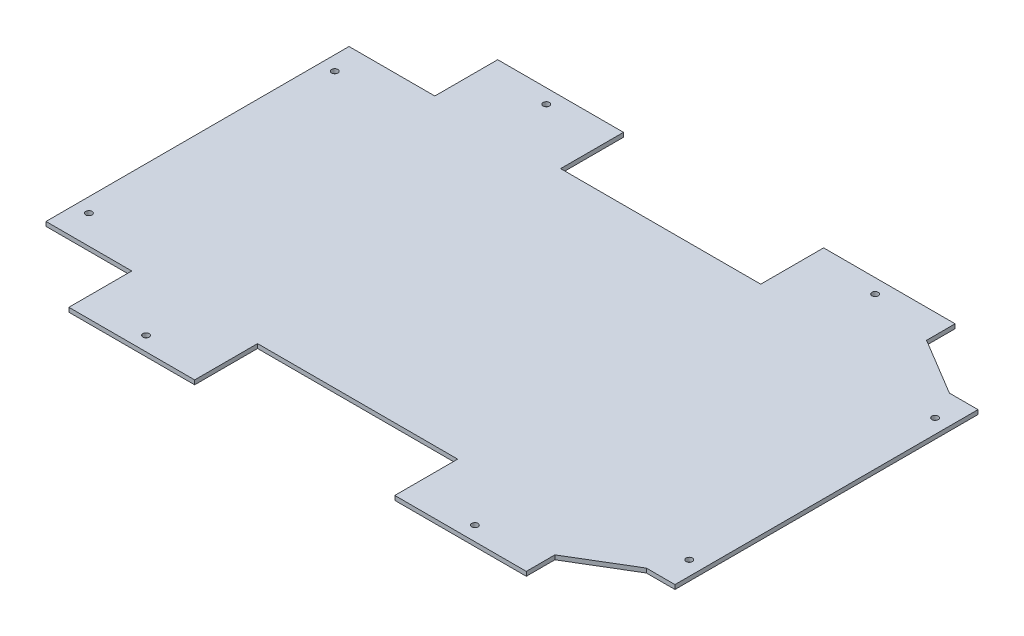
SolidWorks part; units mm, degrees
ref_plane "Plan de face" through (0, 0, 0) normal (0, 0, 1) x (1, 0, 0)
ref_plane "Plan de dessus" through (0, 0, 0) normal (0, 1, 0) x (1, 0, 0)
ref_plane "Plan de droite" through (0, 0, 0) normal (1, 0, 0) x (0, 0, -1)
sketch "Esquisse4" plane through (0, 0, 0) normal (0, 1, 0) x (1, 0, 0)
  line L99 (197.8097, 105.7379) -> (157.8097, 129.7379)
  line L161 (217.8097, 105.7379) -> (197.8097, 105.7379)
  line L163 (-74.1903, 149.7379) -> (-162.1903, 149.7379)
  line L164 (-74.1903, 105.7379) -> (-74.1903, 149.7379)
  line L165 (-162.1903, 105.7379) -> (-222.1903, 105.7379)
  line L166 (-162.1903, 105.7379) -> (-162.1903, 149.7379)
  line L167 (65.8097, 105.7379) -> (-74.1903, 105.7379)
  line L168 (157.8097, 129.7379) -> (157.8097, 149.7379)
  line L169 (65.8097, 105.7379) -> (65.8097, 149.7379)
  line L170 (157.8097, 149.7379) -> (65.8097, 149.7379)
  line L171 (217.8097, -106.2621) -> (217.8097, 105.7379)
  line L172 (-222.1903, 105.7379) -> (-222.1903, -106.2621)
  line L173 (197.8097, -106.2621) -> (217.8097, -106.2621)
  line L174 (-162.1903, -106.2621) -> (-162.1903, -150.2621)
  line L175 (-222.1903, -106.2621) -> (-162.1903, -106.2621)
  line L176 (197.8097, -106.2621) -> (157.8097, -130.2621)
  line L177 (-162.1903, -150.2621) -> (-74.1903, -150.2621)
  line L178 (157.8097, -130.2621) -> (157.8097, -150.2621)
  line L179 (65.8097, -150.2621) -> (157.8097, -150.2621)
  line L180 (65.8097, -106.2621) -> (65.8097, -150.2621)
  line L181 (-74.1903, -106.2621) -> (65.8097, -106.2621)
  line L182 (-74.1903, -106.2621) -> (-74.1903, -150.2621)
  dimension "D1" = 60
  dimension "D2" = 88
  dimension "D3" = 140
  dimension "D4" = 92
  dimension "D5" = 222.1903
  dimension "D6" = 212
  dimension "D7" = 20
  dimension "D8" = 20
  dimension "D9" = 440
extrude "Boss.-Extru.1" add sketch "Esquisse4" along normal blind 3
sketch "Esquisse5" plane through (0, 0, 0) normal (0, -1, 0) x (1, 0, 0)
  line L0 (157.8097, -139.7379) -> (-162.1903, -139.7379) construction
  line L1 (157.8097, -129.7379) -> (157.8097, -149.7379) construction
  line L2 (-162.1903, -149.7379) -> (-162.1903, -105.7379) construction
  line L3 (157.8097, 140.2621) -> (-162.1903, 140.2621) construction
  line L5 (-162.1903, 106.2621) -> (-162.1903, 150.2621) construction
  line L6 (-212.1903, -105.7379) -> (-212.1903, 106.2621) construction
  line L7 (-162.1903, -105.7379) -> (-222.1903, -105.7379) construction
  line L8 (-222.1903, 106.2621) -> (-162.1903, 106.2621) construction
  line L9 (197.8097, 106.2621) -> (217.8097, 106.2621) construction
  line L10 (207.8097, 106.2621) -> (207.8097, -105.7379) construction
  line L15 (217.8097, -105.7379) -> (197.8097, -105.7379) construction
  line L16 (217.8097, 106.2621) -> (217.8097, -105.7379) construction
  line L17 (65.8097, 150.2621) -> (157.8097, 150.2621) construction
  line L18 (-222.1903, -105.7379) -> (-222.1903, 106.2621) construction
  dimension "D1" = 10
  dimension "D2" = 10
  dimension "D3" = 10
hole_wizard "Dégagement M41" positions "Esquisse7" profile "Esquisse6" hole size "M4" standard "Din"
sketch "Esquisse7" plane through (0, 0, 0) normal (0, -1, 0) x (-1, 0, 0)
  line L1 (212.1903, 139.7379) -> (-207.8097, 139.7379) construction
  line L2 (212.1903, 139.7379) -> (212.1903, -140.2621) construction
  line L3 (212.1903, -140.2621) -> (-207.8097, -140.2621) construction
  line L4 (-207.8097, 139.7379) -> (-207.8097, -140.2621) construction
  line L5 (222.1903, 105.7379) -> (222.1903, -106.2621) construction
  line L6 (74.1903, 149.7379) -> (162.1903, 149.7379) construction
  line L7 (-217.8097, -106.2621) -> (-217.8097, 105.7379) construction
  line L8 (-65.8097, -150.2621) -> (-157.8097, -150.2621) construction
  line L9 (-217.8097, 105.7379) -> (-197.8097, 105.7379) construction
  line L10 (-197.8097, -106.2621) -> (-217.8097, -106.2621) construction
  line L11 (222.1903, -106.2621) -> (162.1903, -106.2621) construction
  line L12 (162.1903, 105.7379) -> (222.1903, 105.7379) construction
  line L13 (-111.8097, 149.7379) -> (-111.8097, -150.2621) construction
  line L14 (-157.8097, 149.7379) -> (-65.8097, 149.7379) construction
  line L16 (118.1903, -150.2621) -> (118.1903, 149.7379) construction
  line L17 (162.1903, -150.2621) -> (74.1903, -150.2621) construction
  point P44 (-207.8097, 85.7379)
  point P46 (-207.8097, -86.2621)
  point P48 (-111.8097, -140.2621)
  point P50 (118.1903, -140.2621)
  point P52 (-111.8097, 139.7379)
  point P54 (118.1903, 139.7379)
  point P56 (212.1903, 85.7379)
  point P58 (212.1903, -86.2621)
  dimension "D1" = 10
  dimension "D2" = 10
  dimension "D3" = 10
  dimension "D4" = 10
  dimension "D5" = 20
  dimension "D6" = 20
  dimension "D7" = 20
  dimension "D8" = 20
sketch "Esquisse6" plane through (207.8097, 0, -85.7379) normal (1, 0, 0) x (0, 0, -1)
  line L0 (0, 0) -> (0, 5)
  line L1 (0, 5) -> (2.2, 5)
  line L2 (2.2, 5) -> (2.2, 0)
  line L5 (2.2, 0) -> (0, 0)
  line L10 (0, 5) -> (-2.2, 5) construction
  line L11 (0, -6.35) -> (0, 107.95) construction
  dimension "Diamètre du perçage" = 4.4
  dimension "Profondeur du perçage" = 5
  dimension "Angle de pointe" = 180
